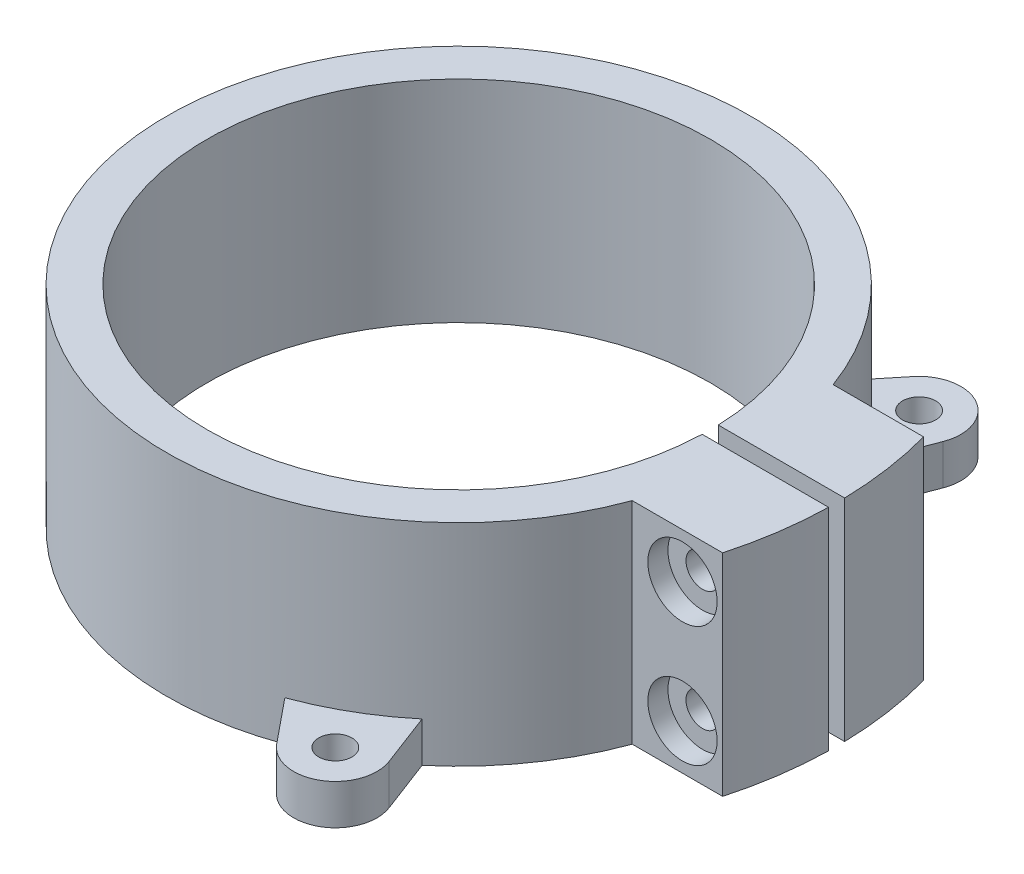
SolidWorks part; units mm, degrees
ref_plane "前视基准面" through (0, 0, 0) normal (0, 0, 1) x (1, 0, 0)
ref_plane "上视基准面" through (0, 0, 0) normal (0, 1, 0) x (1, 0, 0)
ref_plane "右视基准面" through (0, 0, 0) normal (1, 0, 0) x (0, 0, -1)
sketch "草图1" plane through (0, 0, 0) normal (0, 0, 1) x (1, 0, 0)
  line L0 (25.05, 10.5) -> (29.05, 10.5)
  line L1 (29.05, 10.5) -> (29.05, -10.5)
  line L2 (29.05, -10.5) -> (25.05, -10.5)
  line L7 (25.05, -10.5) -> (25.05, 10.5)
  line L8 (0, 0) -> (0, 21.2909) construction
  point P2 (23, 0.1026)
  point P5 (29.05, 0)
  point P11 (0, 0)
  dimension "D1" = 21
  dimension "D2" = 25.05
  dimension "D5" = 4
revolve "旋转1" add sketch "草图1" angle 360 about L8
sketch "草图3" plane through (0, 10.5, 0) normal (0, 1, 0) x (1, 0, 0)
  line L1 (27.2746, 10) -> (36.2746, 10)
  line L2 (27.2746, 10) -> (27.2746, -10)
  line L3 (27.2746, -10) -> (36.2746, -10)
  circle A0 centre (0, 0) radius 29.05 construction
  arc A1 (36.2746, 10) -> (36.2746, -10) centre (0, 0) cw
  point P6 (34.0303, -9.0811)
  point P7 (0, 0)
  point P11 (0, 0)
  point P12 (38.3816, -9.77)
  point P13 (0, 0)
  point P14 (0, 0)
  point P15 (0, 0)
  dimension "D1" = 20
  dimension "D2" = 9
extrude "凸台-拉伸2" add sketch "草图3" against normal through all
sketch "草图2" plane through (0, 10.5, 0) normal (0, 1, 0) x (1, 0, 0)
  line L1 (24.9471, -0.8) -> (37.6277, -0.8)
  line L2 (24.9471, -0.8) -> (24.9471, 0.8)
  line L3 (24.9471, 0.8) -> (37.6277, 0.8)
  line L4 (37.6277, -0.8) -> (37.6277, 0.8)
  line L5 (24.9471, -0.8) -> (37.6277, 0.8) construction
  line L6 (24.9471, 0.8) -> (37.6277, -0.8) construction
  arc A3 (36.2746, -10) -> (36.2746, 10) centre (0, 0) ccw construction
  point P0 (31.2874, 0)
  point P5 (22.55, 0)
  point P6 (24.4546, 0.8)
  point P7 (24.9471, 0.8)
  point P8 (0, 0)
  point P10 (26.9381, 0.8)
  point P11 (29.0583, 0.8)
  point P15 (22.5858, 0.8)
  dimension "D1" = 1.6
extrude "切除-拉伸1" cut sketch "草图2" against normal through all and the other way through all
sketch "草图4" plane through (0, 0, 10) normal (0, 0, 1) x (1, 0, 0)
  line L0 (36.2746, -10.5) -> (36.2746, 10.5) construction
  line L1 (32.2746, 6) -> (32.2746, -6) construction
  circle A0 centre (32.2746, 6) radius 1.65
  circle A1 centre (32.2746, -6) radius 1.65
  point P2 (32.2746, 0)
  point P5 (36.2746, 0)
  dimension "D2" = 3.3
  dimension "D1" = 4
  dimension "D3" = 12
extrude "切除-拉伸2" cut sketch "草图4" against normal through all
sketch "草图5" plane through (0, 0, -10) normal (0, 0, -1) x (-1, 0, 0)
  line L1 (-30.658, 8.8) -> (-33.8912, 8.8)
  line L2 (-33.8912, 8.8) -> (-35.5077, 6)
  line L3 (-35.5077, 6) -> (-33.8912, 3.2)
  line L4 (-33.8912, 3.2) -> (-30.658, 3.2)
  line L5 (-30.658, 3.2) -> (-29.0414, 6)
  line L6 (-29.0414, 6) -> (-30.658, 8.8)
  line L7 (-30.658, -3.2) -> (-33.8912, -3.2)
  line L8 (-33.8912, -3.2) -> (-35.5077, -6)
  line L9 (-35.5077, -6) -> (-33.8912, -8.8)
  line L10 (-33.8912, -8.8) -> (-30.658, -8.8)
  line L11 (-30.658, -8.8) -> (-29.0414, -6)
  line L12 (-29.0414, -6) -> (-30.658, -3.2)
  circle A0 centre (-32.2746, 6) radius 2.8 construction
  circle A1 centre (-32.2746, -6) radius 2.8 construction
  dimension "D1" = 5.6
extrude "切除-拉伸3" cut sketch "草图5" against normal blind 2
sketch "草图6" plane through (0, 0, 10) normal (0, 0, 1) x (1, 0, 0)
  circle A0 centre (32.2746, -6) radius 1.65 construction
  circle A1 centre (32.2746, 6) radius 1.65 construction
  circle A2 centre (32.2746, -6) radius 1.65
  circle A3 centre (32.2746, 6) radius 1.65
  circle A4 centre (32.2746, -6) radius 3.45
  circle A5 centre (32.2746, 6) radius 3.45
  dimension "D1" = 1.8
extrude "切除-拉伸4" cut sketch "草图6" against normal blind 2
sketch "草图7" plane through (0, -10.5, 0) normal (0, -1, 0) x (1, 0, 0)
  line L0 (-34.2113, 4.097) -> (-28.6165, 5)
  line L1 (-34.2113, -4.097) -> (-28.6165, -5)
  line L2 (20.6537, 27.5793) -> (18.6384, 22.2826)
  line L3 (13.5575, 31.6763) -> (9.9781, 27.2826)
  line L4 (13.5575, -31.6763) -> (9.9781, -27.2826)
  line L5 (20.6537, -27.5793) -> (18.6384, -22.2826)
  circle A0 centre (-33.55, 0) radius 1.65
  arc A1 (27.2746, 10) -> (27.2746, -10) centre (0, 0) ccw construction
  arc A2 (-34.2113, 4.097) -> (-34.2113, -4.097) centre (-33.55, 0) ccw
  arc A3 (-28.6165, 5) -> (-28.6165, -5) centre (0, 0) ccw
  arc A4 (18.6384, 22.2826) -> (9.9781, 27.2826) centre (0, 0) ccw
  arc A5 (20.6537, 27.5793) -> (13.5575, 31.6763) centre (16.775, 29.0552) ccw
  circle A6 centre (16.775, 29.0552) radius 1.65
  arc A7 (9.9781, -27.2826) -> (18.6384, -22.2826) centre (0, 0) ccw
  arc A8 (13.5575, -31.6763) -> (20.6537, -27.5793) centre (16.775, -29.0552) ccw
  circle A9 centre (16.775, -29.0552) radius 1.65
  point P24 (0, 0)
  dimension "D1" = 3.3
  dimension "D2" = 4.5
  dimension "D3" = 2.5
  dimension "D4" = 10
  dimension "D5" = 3
extrude "凸台-拉伸3" add sketch "草图7" against normal blind 4
